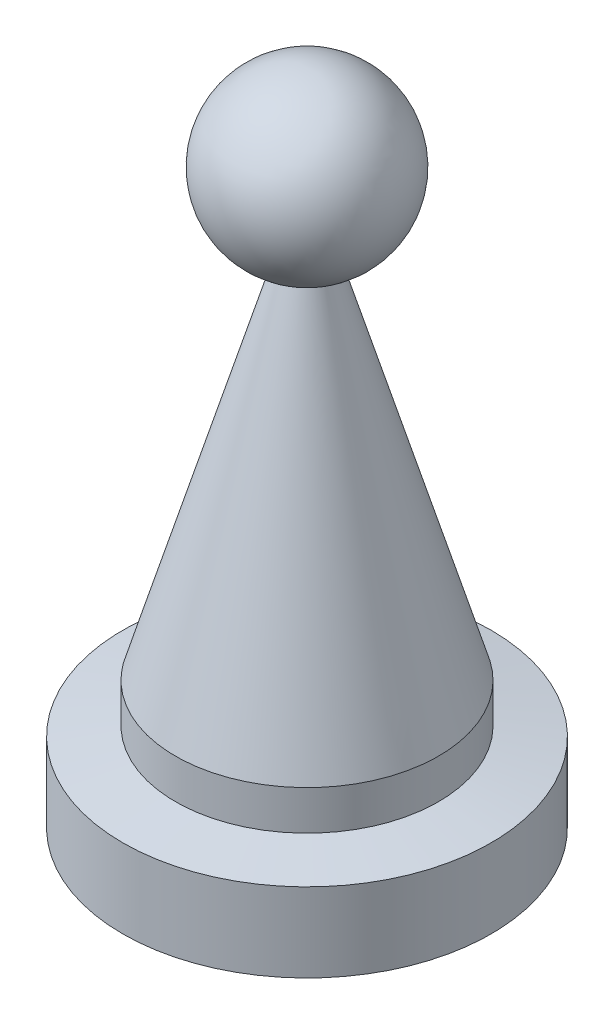
SolidWorks part; units mm, degrees
material "Beech"
ref_plane "Front Plane" through (0, 0, 0) normal (0, 0, 1) x (1, 0, 0)
ref_plane "Top Plane" through (0, 0, 0) normal (0, 1, 0) x (1, 0, 0)
ref_plane "Right Plane" through (0, 0, 0) normal (1, 0, 0) x (0, 0, -1)
sketch "Sketch1" plane through (0, 0, 0) normal (0, 0, 1) x (1, 0, 0)
  line L0 (0, 0) -> (0, 25)
  line L1 (0, 0) -> (7, 0)
  line L2 (7, 0) -> (7, 3)
  line L3 (7, 3) -> (5, 3.3527)
  line L4 (5, 3.3527) -> (5, 4.8527)
  line L5 (5, 4.8527) -> (0.9222, 18.6336)
  arc A0 (0.9222, 18.6336) -> (0, 25) centre (0, 21.75) ccw
  dimension "D7" = 3.25
  dimension "D1" = 25
  dimension "D2" = 7
  dimension "D3" = 3
  dimension "D4" = 2
  dimension "D5" = 100
  dimension "D6" = 1.5
revolve "Revolve1" add sketch "Sketch1" angle 360 about L0
